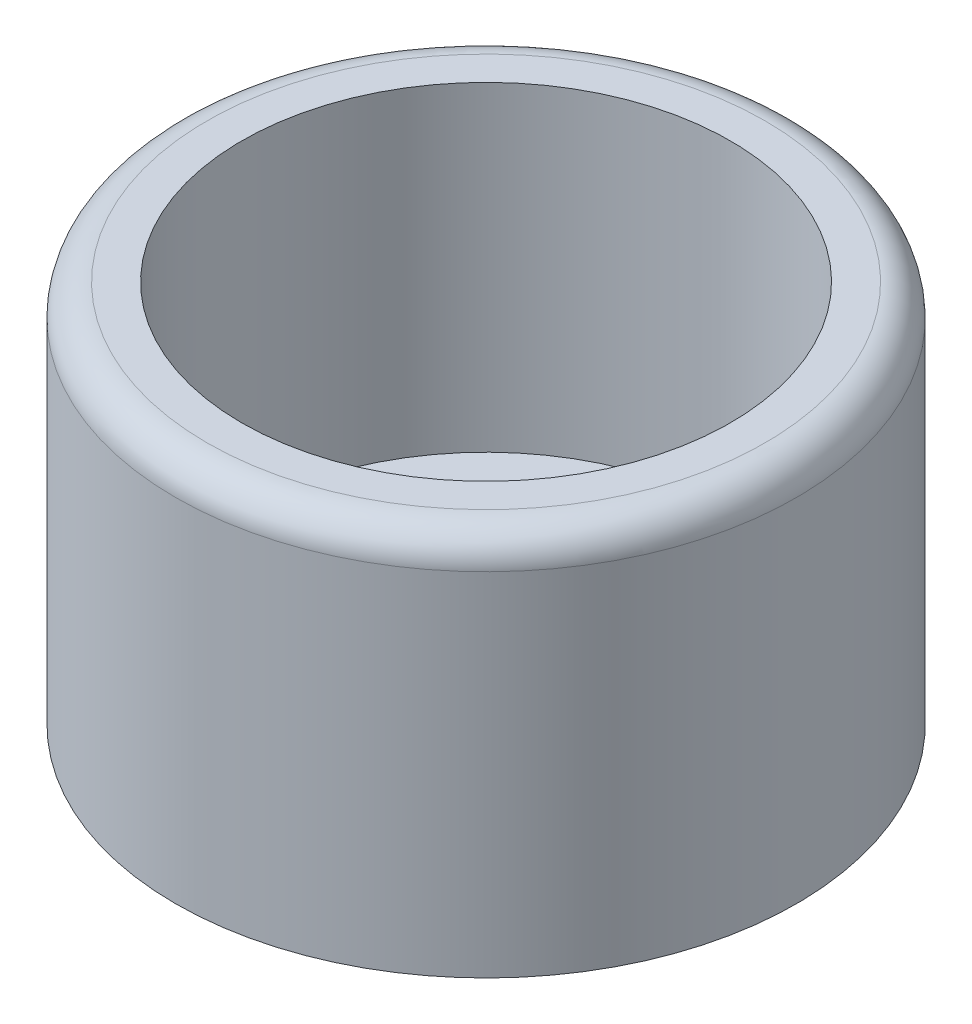
SolidWorks part; units mm, degrees
ref_plane "Спереди" through (0, 0, 0) normal (0, 0, 1) x (1, 0, 0)
ref_plane "Сверху" through (0, 0, 0) normal (0, 1, 0) x (1, 0, 0)
ref_plane "Справа" through (0, 0, 0) normal (1, 0, 0) x (0, 0, -1)
sketch "Эскиз1" plane through (0, 0, 0) normal (0, 1, 0) x (1, 0, 0)
  circle A0 centre (0, 0) radius 4.925
  dimension "D1" = 9.85
extrude "Бобышка-Вытянуть1" add sketch "Эскиз1" along normal blind 6.08
sketch "Эскиз2" plane through (0, 6.08, 0) normal (0, 1, 0) x (1, 0, 0)
  circle A0 centre (0, 0) radius 3.875
  dimension "D1" = 7.75
extrude "Вырез-Вытянуть1" cut sketch "Эскиз2" against normal offset from surface (5.08 mm away) 1 up to face at (0, 0, 4.925)
fillet "Скругление1" radius 0.5 1 edges at (0, 6.08, 4.925)
sketch "Эскиз3" plane through (0, 1, 0) normal (0, 1, 0) x (1, 0, 0)
  line L0 (0, 3.875) -> (0, -3.875) construction
  line L1 (-3.875, 0) -> (3.875, 0) construction
  line L2 (2.875, 0.5) -> (0.5, 0.5)
  line L3 (2.875, -0.5) -> (0.5, -0.5)
  line L4 (0.5, 2.875) -> (0.5, 0.5)
  line L5 (-0.5, 2.875) -> (-0.5, 0.5)
  line L6 (0.5, -0.5) -> (0.5, -2.875)
  line L7 (-0.5, 0.5) -> (-2.875, 0.5)
  line L8 (-0.5, -0.5) -> (-0.5, -2.875)
  line L9 (-0.5, -0.5) -> (-2.875, -0.5)
  circle A0 centre (0, 0) radius 3.875 construction
  circle A1 centre (0, 0) radius 3.875 construction
  arc A2 (0.5, 2.875) -> (-0.5, 2.875) centre (0, 2.875) ccw
  arc A3 (0.5, -2.875) -> (-0.5, -2.875) centre (0, -2.875) cw
  arc A4 (2.875, -0.5) -> (2.875, 0.5) centre (2.875, 0) ccw
  arc A5 (-2.875, 0.5) -> (-2.875, -0.5) centre (-2.875, 0) ccw
  dimension "D1" = 1
  dimension "D2" = 1
  dimension "D3" = 1
  dimension "D4" = 1
extrude "Вырез-Вытянуть2" cut sketch "Эскиз3" against normal through all
